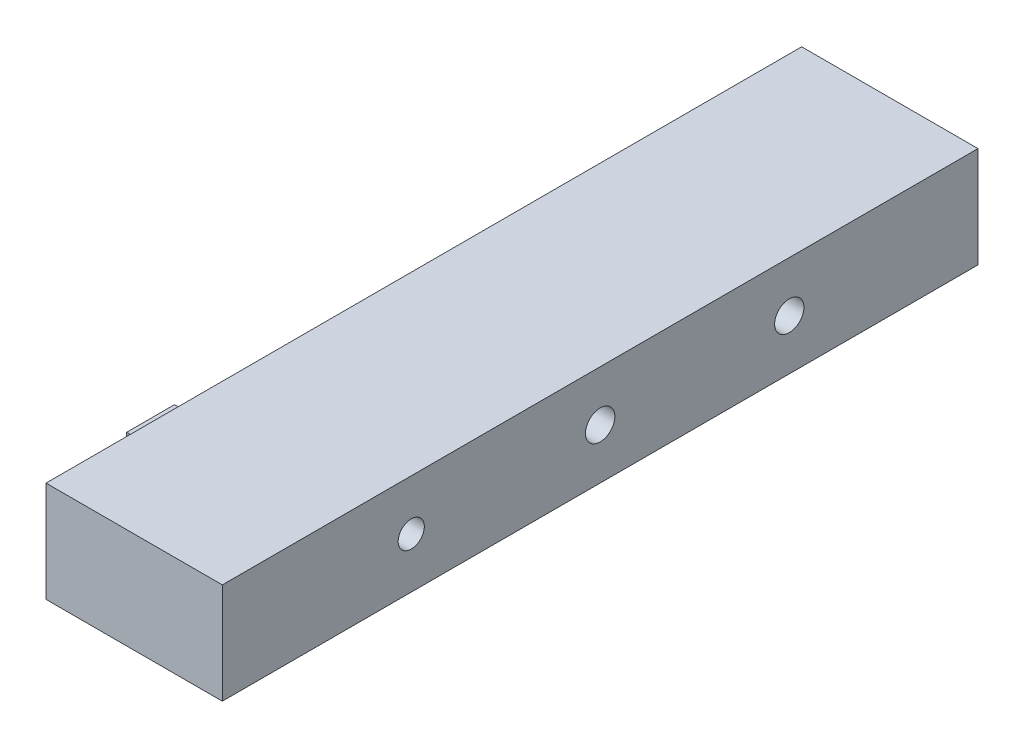
SolidWorks part; units mm, degrees
ref_plane "Front Plane" through (0, 0, 0) normal (0, 0, 1) x (1, 0, 0)
ref_plane "Top Plane" through (0, 0, 0) normal (0, 1, 0) x (1, 0, 0)
ref_plane "Right Plane" through (0, 0, 0) normal (1, 0, 0) x (0, 0, -1)
sketch "Sketch1" plane through (0, 0, 0) normal (1, 0, 0) x (0, 0, -1)
  line L1 (0, 0) -> (30, 0)
  line L2 (0, 0) -> (0, 4)
  line L3 (0, 4) -> (30, 4)
  line L4 (30, 0) -> (30, 4)
  dimension "D1" = 30
  dimension "D2" = 4
extrude "Boss-Extrude1" add sketch "Sketch1" along normal blind 7
sketch "Sketch2" plane through (0, 0, 0) normal (1, 0, 0) x (0, 0, -1)
  line L0 (0, 2) -> (4.0354, 2)
  line L1 (0, 4) -> (0, 0) construction
  line L2 (4.0354, 0) -> (4.0354, 1.1939)
  line L3 (0, 0) -> (30, 0) construction
  line L4 (4.0354, 4) -> (4.0354, 2.9523)
  line L5 (30, 4) -> (0, 4) construction
  line L7 (4.2006, 3.1462) -> (6.1006, 3.1462)
  line L8 (4.2006, 3.1462) -> (4.2006, 1.2462)
  line L9 (4.2006, 1.2462) -> (6.1006, 1.2462)
  line L10 (6.1006, 3.1462) -> (6.1006, 1.2462)
  dimension "D1" = 1.9
  dimension "D2" = 1.9
extrude "Boss-Extrude2" add sketch "Sketch2" against normal blind 1 contours L8 L7 L10 L9
sketch "Sketch3" plane through (0, 0, 0) normal (1, 0, 0) x (0, 0, -1)
  line L0 (30, 2) -> (25.8692, 2)
  line L3 (25.7069, 2.9038) -> (23.8069, 2.9038)
  line L5 (25.7069, 2.9038) -> (25.7069, 1.1344)
  line L16 (30, 0) -> (30, 4) construction
  line L17 (23.8069, 2.9038) -> (25.7069, 2.9038)
  line L19 (23.8069, 2.9038) -> (23.8069, 1.1344)
  line L21 (25.7069, 1.1344) -> (23.8069, 1.1344)
  line L22 (23.8069, 2.9038) -> (23.8069, 1.1344)
  line L23 (23.8069, 1.1344) -> (25.7069, 1.1344)
  line L24 (25.7069, 2.9038) -> (25.7069, 1.1344)
  dimension "D1" = 1.9
  dimension "D2" = 1.7694
extrude "Boss-Extrude3" add sketch "Sketch3" against normal blind 1 and the other way blind 1 contours L5 L3 L22 L21
sketch "Sketch4" plane through (7, 0, 0) normal (1, 0, 0) x (0, 0, -1)
  circle A0 centre (7.5, 2) radius 0.5192
  circle A1 centre (15, 2) radius 0.5838
  circle A2 centre (22.5085, 2) radius 0.5816
extrude "Cut-Extrude2" cut sketch "Sketch4" along normal blind 1 and the other way blind 3
